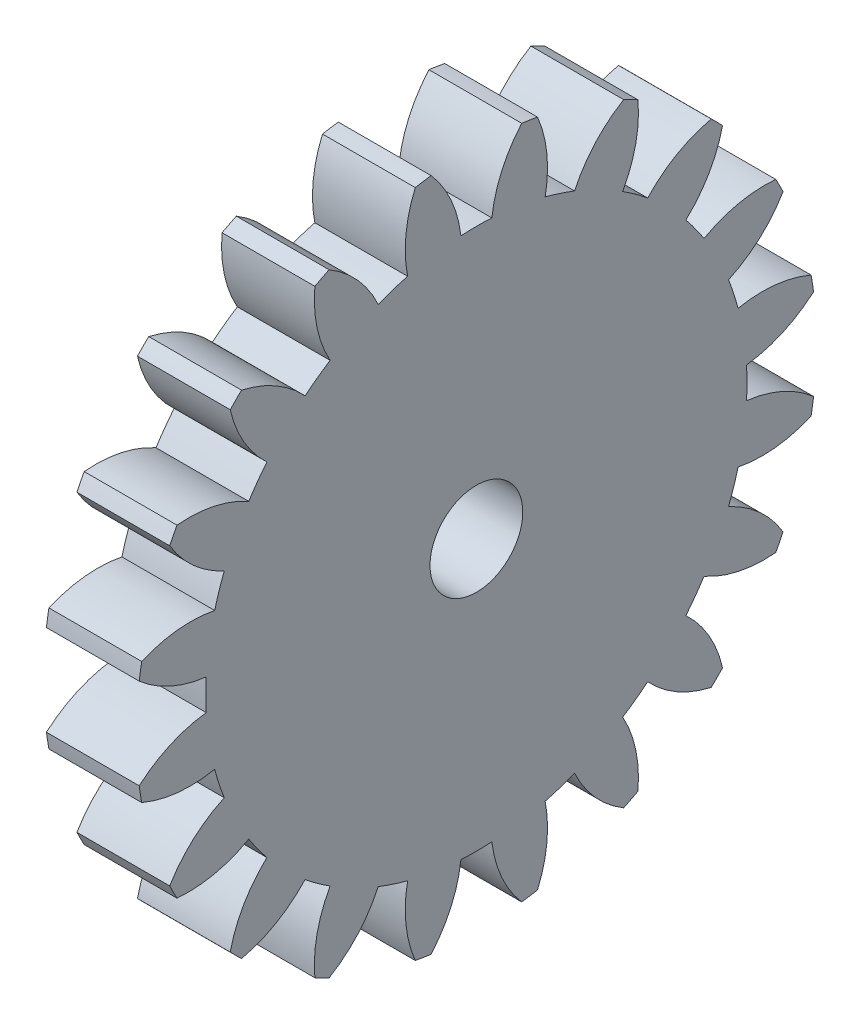
SolidWorks part; units mm, degrees
ref_plane "Plane1" through (0, 0, 0) normal (0, 0, 1) x (1, 0, 0)
ref_plane "Plane2" through (0, 0, 0) normal (0, 1, 0) x (1, 0, 0)
ref_plane "Plane3" through (0, 0, 0) normal (1, 0, 0) x (0, 0, -1)
sketch "HoldingSke" plane through (0, 0, 0) normal (0, 1, 0) x (1, 0, 0)
  line L0 (0, 0) -> (0.9397, -0.342)
  line L1 (-15, 0) -> (100, 0) construction
  line L2 (0, 0) -> (-2.1039, 2.3779)
  line L3 (0, 0) -> (-11.863, 4.5341)
  line L4 (0, 0) -> (8.1152, 2.9537)
  line L5 (0, 0) -> (-46.8476, -17.4728)
  line L6 (0, 0) -> (-2.4869, -1.6779)
  line L7 (-2.1039, 2.3779) -> (8.6586, 51.2059)
  line L8 (-76.2, 54.61) -> (-75.7, 54.61)
  line L9 (-71.009, 38.7566) -> (-53.1078, 45.2721)
  line L10 (-76.2, 71.12) -> (104.1128, 71.12)
  line L11 (0, 0) -> (-3, 0)
  line L12 (-76.2, 101.6) -> (-76.162, 101.6)
  line L13 (24.9733, 27.94) -> (52.9518, 28.4284)
  line L14 (24.9733, 27.94) -> (24.9743, 27.94)
  line L15 (24.9733, 27.94) -> (100.4006, 29.5858)
  line L16 (-63.627, -1) -> (-12.827, -1)
  circle A0 centre (0, 0) radius 1.5
  circle A1 centre (0, 0) radius 8.749
  circle A2 centre (0, 0) radius 37.5
  circle A3 centre (0, 0) radius 1.5
  dimension "MHD" = 17.498
  dimension "Hub_dia" = 75
  dimension "Bore" = 3
  dimension "MBD" = 3
  dimension "Num_teeth" = 20
  dimension "Pitch" = 1
  dimension "Overall_len" = 50
  dimension "Show_teeth" = 20
  dimension "Thickness" = 3
  dimension "OAL" = 50.0001
  dimension "T_dim" = 0.5
  dimension "Ap" = 20
  dimension "H" = 19.05
  dimension "Pitch_radius" = 180.3128
  dimension "Width" = 3
  dimension "Backlash" = 0.038
  dimension "Addendum_fac" = 1
  dimension "Dedendum_fac" = 1.25
  dimension "Clearance_fac" = 0.25
  dimension "Dedendum_add" = 0.001
  dimension "Module" = 1
sketch "BasProSke" plane through (0, 0, 0) normal (0, 1, 0) x (1, 0, 0)
  line L0 (-10, 0) -> (60, 0) construction
  line L1 (0, 0) -> (0, 11)
  line L2 (0, 0) -> (3, 0)
  line L3 (3, 0) -> (3, 11)
  line L4 (3, 11) -> (0, 11)
  dimension "Thickness" = 3
  dimension "Diameter" = 22
revolve "Base-Revolve" add sketch "BasProSke" angle 360 about L0
sketch "TooCutSke" plane through (0, 0, 0) normal (1, 0, 0) x (0, 0, -1)
  line L1 (0, 0) -> (0, 107) construction
  line L2 (0, 0) -> (-0.8511, 9.9637) construction
  line L3 (0, 0) -> (-3.1206, 19.7028) construction
  line L4 (-0.8511, 9.9637) -> (-1.5603, 9.8514) construction
  arc A0 (0.4999, 8.7347) -> (-0.4999, 8.7347) centre (0, 0) ccw
  arc A1 (1.4852, 10.9249) -> (-1.4852, 10.9249) centre (0, 0) ccw
  circle A2 centre (0, 0) radius 10 construction
  circle A3 centre (0, 0) radius 9.3969 construction
  arc A4 (-0.4999, 8.7347) -> (-1.4852, 10.9249) centre (-4.4722, 8.2645) ccw
  arc A5 (1.4852, 10.9249) -> (0.4999, 8.7347) centre (4.4722, 8.2645) ccw
  dimension "Root_dia" = 17.498
  dimension "Overcut_dia" = 22.0508
  dimension "Pitch_dia" = 20
  dimension "Base_dia" = 18.7939
  dimension "Flank_rad" = 4
  dimension "Half_ang" = 9
  dimension "Half_CT" = 0.7181
extrude "ToothCut" cut sketch "TooCutSke" along normal through all
fillet "Breaks" [suppressed] radius 0.02
fillet "RootFillets" [suppressed] radius 0.251
pattern_circular "TeethCuts" count 20 every 18 about axis through (-10, 0, 0) along (1, 0, 0) of "ToothCut", "RootFillets", "Breaks"
sketch "HubNeaOneSke" plane through (0, 0, 0) normal (-1, 0, 0) x (0, 0, 1)
  circle A0 centre (0, 0) radius 8.749
  dimension "Diameter" = 17.498
extrude "HubNearOne" [suppressed] add sketch "HubNeaOneSke" along normal blind 47.0001
sketch "HubNeaBotSke" plane through (0, 0, 0) normal (-1, 0, 0) x (0, 0, 1)
  circle A0 centre (0, 0) radius 8.749
  dimension "Diameter" = 17.498
extrude "HubNearBoth" [suppressed] add sketch "HubNeaBotSke" along normal blind 23.5
ref_plane "FarPln" through (3, 0, 0) normal (1, 0, 0) x (0, 0, -1)
sketch "HubFarSke" plane through (3, 0, 0) normal (1, 0, 0) x (0, 0, -1)
  circle A0 centre (0, 0) radius 8.749
  dimension "Diameter" = 17.498
extrude "HubFar" [suppressed] add sketch "HubFarSke" along normal blind 23.5
sketch "BorSke" plane through (0, 0, 0) normal (1, 0, 0) x (0, 0, -1)
  circle A0 centre (0, 0) radius 1.5
  dimension "Diameter" = 3
extrude "Bore" cut sketch "BorSke" along normal mid plane 100.0001
sketch "KeySke" plane through (0, 0, 0) normal (1, 0, 0) x (0, 0, -1)
  line L0 (-0.6, 0) -> (-0.6, 2)
  line L1 (-0.6, 2) -> (0.6, 2)
  line L2 (0.6, 2) -> (0.6, 0)
  line L3 (0, 0) -> (0, 34) construction
  line L4 (-0.6, 0) -> (0.6, 0)
  dimension "Offset" = 2
  dimension "Width" = 1.2
extrude "Keyway" [suppressed] cut sketch "KeySke" along normal mid plane 100.0001
pattern_circular "Keyway2" [suppressed] count 2 every 90 about axis through (-10, 0, 0) along (1, 0, 0)
equation "' \"Module@HoldingSke\" = 6.35"
equation "' \"Num_teeth@HoldingSke\" = 12"
equation "' \"Ap@HoldingSke\" =  20"
equation "' \"Ap@HoldingSke\" = 20"
equation "' \"Width@HoldingSke\" = 0.5 * 25.4"
equation "' \"Hub_dia@HoldingSke\"= 1 * 25.4"
equation "' \"Hub_dia@HoldingSke\" = 1 * 25.4"
equation "' \"Overall_len@HoldingSke\" = 1.0 * 25.4"
equation "' \"Bore@HoldingSke\" = 0.75 * 25.4"
equation "' \"T_dim@HoldingSke\" = 0.1 * 25.4"
equation "' \"Width@KeySke\" = 0.25 * 25.4"
equation "' \"Show_teeth@HoldingSke\" = 13"
equation "' \"Backlash@HoldingSke\" = 0.009 * 25.4"
equation "' \"Addendum_fac@HoldingSke\" = 1.0"
equation "' \"Dedendum_fac@HoldingSke\" = 1.25"
equation "' \"Dedendum_add@HoldingSke\" = 0.00005 * 25.4"
equation "' \"Clearance_fac@HoldingSke\" = 0.25"
equation "\"Pitch@HoldingSke\" = 1 / \"Module@HoldingSke\""
equation "\"Overcut_dia@TooCutSke\" = (\"Num_teeth@HoldingSke\" + 2 * \"Addendum_fac@HoldingSke\") / \"Pitch@HoldingSke\" + 0.002 * 25.4"
equation "\"Pitch_dia@TooCutSke\" = \"Num_teeth@HoldingSke\" / \"Pitch@HoldingSke\""
equation "\"Base_dia@TooCutSke\" = \"Num_teeth@HoldingSke\" / \"Pitch@HoldingSke\" * cos((\"Ap@HoldingSke\"  * 3.14159265 / 180))"
equation "\"Root_dia@TooCutSke\" = (\"Num_teeth@HoldingSke\" + 2) / \"Pitch@HoldingSke\" - 2 * (\"Addendum_fac@HoldingSke\" + \"Dedendum_fac@HoldingSke\") / \"Pitch@HoldingSke\" - \"Dedendum_add@HoldingSke\" * 2"
equation "\"Half_ang@TooCutSke\" = 180 / \"Num_teeth@HoldingSke\""
equation "\"Half_CT@TooCutSke\" = \"Num_teeth@HoldingSke\" / \"Pitch@HoldingSke\" * sin((3.14159265 / 2 / \"Num_teeth@HoldingSke\")) / 2 - 7 * \"Backlash@HoldingSke\" / 4"
equation "\"Flank_rad@TooCutSke\" = \"Num_teeth@HoldingSke\" / \"Pitch@HoldingSke\" / 5"
equation "\"Radius@RootFillets\" = \"Clearance_fac@HoldingSke\" / \"Pitch@HoldingSke\" + \"Dedendum_add@HoldingSke\""
equation "\"Break_rad@Breaks\" = 0.02 / \"Pitch@HoldingSke\""
equation "\"Thickness@HoldingSke\" = \"Width@HoldingSke\""
equation "\"OAL@HoldingSke\" = \"Thickness@HoldingSke\""
equation "\"MHD@HoldingSke\" = (\"Num_teeth@HoldingSke\" + 2) / \"Pitch@HoldingSke\" - 2 * (\"Addendum_fac@HoldingSke\" + \"Dedendum_fac@HoldingSke\")  / \"Pitch@HoldingSke\" - \"Dedendum_add@HoldingSke\" * 2"
equation "\"MBD@HoldingSke\" = (\"Num_teeth@HoldingSke\" + 2) / \"Pitch@HoldingSke\" - 2 * (\"Addendum_fac@HoldingSke\" + \"Dedendum_fac@HoldingSke\")  / \"Pitch@HoldingSke\" - \"Dedendum_add@HoldingSke\" * 2 - 0.002 * 25.4"
equation "\"MHD@HoldingSke\" = ((sgn( \"MHD@HoldingSke\" - \"Hub_dia@HoldingSke\" )-1)*( \"MHD@HoldingSke\" - \"Hub_dia@HoldingSke\" ))/-2+ \"Hub_dia@HoldingSke\""
equation "\"MBD@HoldingSke\" = ((sgn( \"MBD@HoldingSke\" - \"Bore@HoldingSke\" )-1)*( \"MBD@HoldingSke\" - \"Bore@HoldingSke\" ))/-2+ \"Bore@HoldingSke\""
equation "\"OAL@HoldingSke\" = ((sgn( \"OAL@HoldingSke\" - \"Overall_len@HoldingSke\" )+1)*( \"OAL@HoldingSke\" - \"Overall_len@HoldingSke\" ))/2 + \"Overall_len@HoldingSke\" + 0.000002 * 25.4"
equation "\"Num_teeth@TeethCuts\" = int( \"Show_teeth@HoldingSke\" ) + 1"
equation "\"Num_teeth@TeethCuts\" = ((sgn( \"Num_teeth@TeethCuts\" - \"Num_teeth@HoldingSke\" )-1)*( \"Num_teeth@TeethCuts\" - \"Num_teeth@HoldingSke\" ))/-2+ \"Num_teeth@HoldingSke\""
equation "\"Num_teeth@TeethCuts\" = ((sgn( \"Num_teeth@TeethCuts\" - 2.0)+1)*( \"Num_teeth@TeethCuts\" - 2.0))/2 +2.0"
equation "\"Angle@TeethCuts\" = 360.0 / \"Num_teeth@HoldingSke\""
equation "\"Diameter@BasProSke\" = (\"Num_teeth@HoldingSke\" + 2 * \"Addendum_fac@HoldingSke\") / \"Pitch@HoldingSke\""
equation "\"Thickness@BasProSke\"  = \"Thickness@HoldingSke\""
equation "' \"Fillet_rad@BasProSke\" =  \"Thickness@HoldingSke\" * 0.05"
equation "' \"Fillet_rad@BasProSke\" = \"Thickness@HoldingSke\" * 0.05"
equation "\"MHD@HoldingSke\" = ((sgn( \"MHD@HoldingSke\" - \"Root_dia@TooCutSke\" )-1)*( \"MHD@HoldingSke\" - \"Root_dia@TooCutSke\" ))/-2+ \"Root_dia@TooCutSke\""
equation "\"Diameter@HubNeaOneSke\" = \"MHD@HoldingSke\""
equation "\"Length@HubNearOne\" = \"OAL@HoldingSke\" - \"Thickness@BasProSke\""
equation "\"Diameter@HubNeaBotSke\" = \"MHD@HoldingSke\""
equation "\"Length@HubNearBoth\" = ( \"OAL@HoldingSke\" - \"Thickness@BasProSke\" ) / 2.0"
equation "\"Thickness@FarPln\" = \"Thickness@BasProSke\""
equation "\"Diameter@HubFarSke\" = \"MHD@HoldingSke\""
equation "\"Length@HubFar\" = ( \"OAL@HoldingSke\" - \"Thickness@BasProSke\" ) / 2.0"
equation "\"Diameter@BorSke\" = \"MBD@HoldingSke\""
equation "\"D1@Bore\" = \"OAL@HoldingSke\" * 2.0"
equation "\"D1@Keyway\" = \"OAL@HoldingSke\" * 2.0"
equation "\"Offset@KeySke\" = \"T_dim@HoldingSke\" + \"MBD@HoldingSke\" / 2.0"
